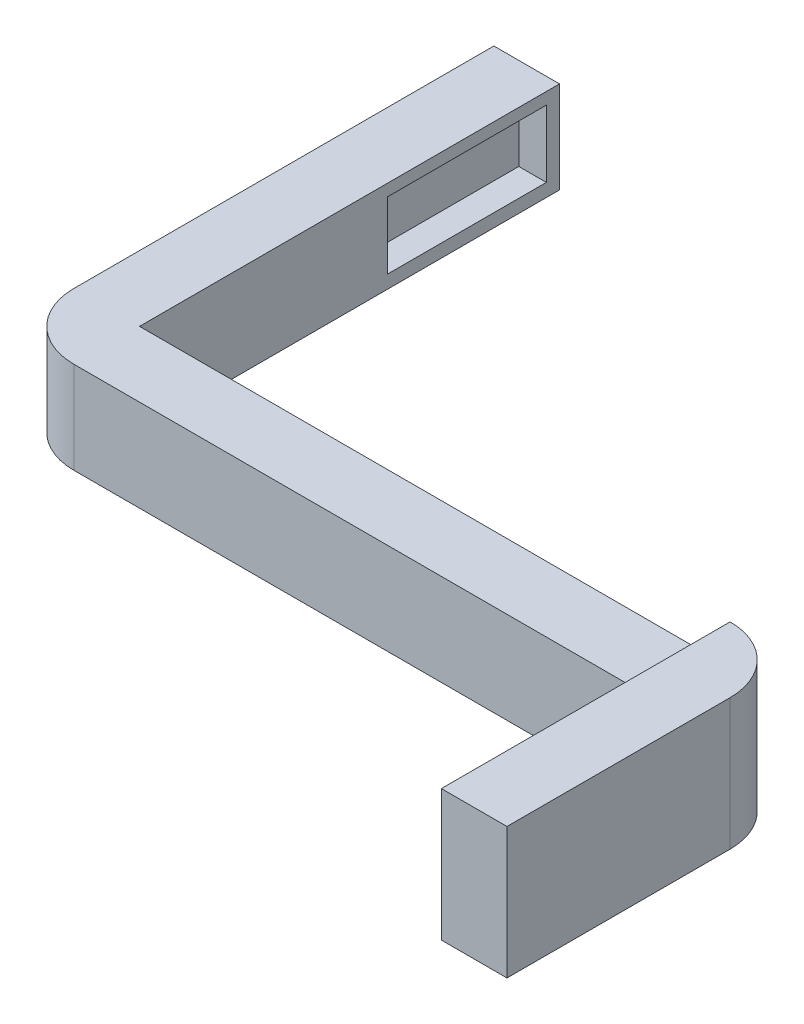
SolidWorks part; units mm, degrees
ref_plane "Front Plane" through (0, 0, 0) normal (0, 0, 1) x (1, 0, 0)
ref_plane "Top Plane" through (0, 0, 0) normal (0, 1, 0) x (1, 0, 0)
ref_plane "Right Plane" through (0, 0, 0) normal (1, 0, 0) x (0, 0, -1)
other "Configuration Table"
sketch "Sketch1" plane through (0, 0, 0) normal (0, 0, 1) x (1, 0, 0)
  line L1 (22.5, 3.5) -> (-22.5, 3.5)
  line L2 (22.5, 3.5) -> (22.5, -3.5)
  line L3 (22.5, -3.5) -> (-22.5, -3.5)
  line L4 (-22.5, 3.5) -> (-22.5, -3.5)
  line L5 (22.5, 3.5) -> (-22.5, -3.5) construction
  line L6 (22.5, -3.5) -> (-22.5, 3.5) construction
  point P0 (0, 0)
  dimension "D1" = 45
  dimension "D2" = 7
extrude "Boss-Extrude1" add sketch "Sketch1" along normal blind 5
sketch "Sketch2" plane through (-22.5, 0, 0) normal (-1, 0, 0) x (0, 0, 1)
  line L0 (5, -3.5) -> (0, -3.5) construction
  line L1 (5, 3.5) -> (-32, 3.5)
  line L2 (5, 3.5) -> (5, -3.5)
  line L3 (5, -3.5) -> (-32, -3.5)
  line L4 (-32, 3.5) -> (-32, -3.5)
  dimension "D1" = 37
extrude "Boss-Extrude2" add sketch "Sketch2" along normal blind 5
fillet "Fillet1" radius 5 1 edges at (-27.5, 0, 5)
sketch "Sketch3" plane through (22.5, 0, 0) normal (1, 0, 0) x (0, 0, -1)
  line L1 (0, 6.5) -> (-22, 6.5)
  line L2 (0, 6.5) -> (0, -3.5)
  line L3 (0, -3.5) -> (-22, -3.5)
  line L4 (-22, 6.5) -> (-22, -3.5)
  line L5 (-5, -3.5) -> (0, -3.5) construction
  line L6 (0, 13.6459) -> (0, -13.6459) construction
  dimension "D1" = 22
  dimension "D2" = 10
extrude "Boss-Extrude3" add sketch "Sketch3" along normal blind 5
fillet "Fillet2" radius 5 1 edges at (27.5, 1.5, 0)
sketch "Sketch4" plane through (-22.5, 0, 0) normal (1, 0, 0) x (0, 0, -1)
  line L1 (32, 3.5) -> (32, -3.5) construction
  line L3 (31, 2.6) -> (18.9, 2.6)
  line L4 (31, 2.6) -> (31, -2.5)
  line L5 (31, -2.5) -> (18.9, -2.5)
  line L6 (18.9, 2.6) -> (18.9, -2.5)
  line L7 (31, 2.6) -> (18.9, -2.5) construction
  line L8 (31, -2.5) -> (18.9, 2.6) construction
  line L9 (32, -3.5) -> (0, -3.5) construction
  point P0 (24.95, 0.05)
  dimension "D1" = 12.1
  dimension "D2" = 5.1
  dimension "D4" = 1
  dimension "D3" = 1
extrude "Cut-Extrude1" cut sketch "Sketch4" against normal blind 2.1
